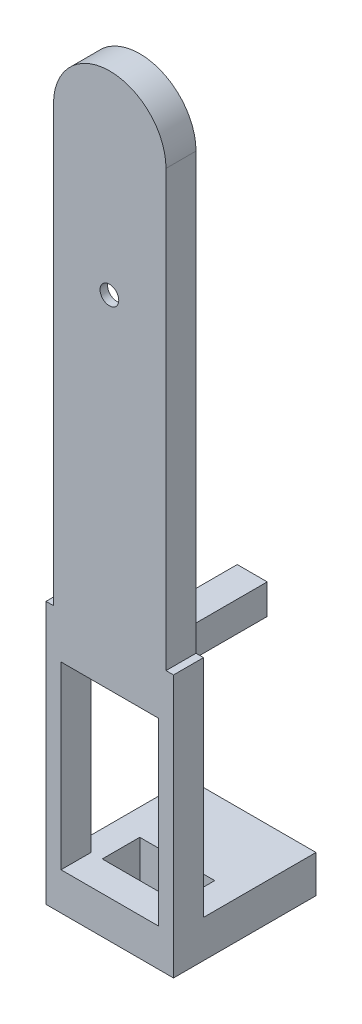
SolidWorks part; units mm, degrees
ref_plane "前基準面" through (0, 0, 0) normal (0, 0, 1) x (1, 0, 0)
ref_plane "上基準面" through (0, 0, 0) normal (0, 1, 0) x (1, 0, 0)
ref_plane "右基準面" through (0, 0, 0) normal (1, 0, 0) x (0, 0, -1)
sketch "草圖1" plane through (0, 0, 0) normal (0, 0, 1) x (1, 0, 0)
  line L0 (0, 0) -> (0, 4.6483) construction
  line L1 (7.5, 0) -> (7.5, 58)
  line L2 (7.5, 0) -> (-7.5, 0)
  line L3 (-7.5, 0) -> (-7.5, 58)
  arc A0 (7.5, 58) -> (-7.5, 58) centre (0, 58) ccw
  dimension "D1" = 7.5
  dimension "D2" = 58
extrude "填料-伸長1" add sketch "草圖1" along normal blind 4
sketch "草圖6" plane through (0, 0, 0) normal (0, 0, 1) x (1, 0, 0)
  line L0 (0, 62.3953) -> (0, -4.428) construction
  line L1 (0, -2.2) -> (0, 2.2) construction
  line L3 (8.5, 0) -> (-8.5, 0)
  line L4 (8.5, 0) -> (8.5, -35)
  line L5 (8.5, -35) -> (-8.5, -35)
  line L6 (-8.5, 0) -> (-8.5, -35)
  dimension "D1" = 17
  dimension "D2" = 8.5
  dimension "D3" = 35
extrude "填料-伸長2" add sketch "草圖6" along normal blind 4
sketch "草圖7" plane through (0, 0, 0) normal (0, 0, 1) x (1, 0, 0)
  line L0 (0, 64.1958) -> (0, -38.5274) construction
  line L1 (0, -10.45) -> (0, 10.45) construction
  line L3 (-6.5, -6) -> (6.5, -6)
  line L4 (-6.5, -6) -> (-6.5, -30)
  line L5 (-6.5, -30) -> (6.5, -30)
  line L6 (6.5, -6) -> (6.5, -30)
  line L7 (-8.5, -35) -> (8.5, -35) construction
  dimension "D1" = 6.5
  dimension "D2" = 13
  dimension "D3" = 24
  dimension "D4" = 5
extrude "除料-伸長3" cut sketch "草圖7" along normal blind 12.1
sketch "草圖8" plane through (0, 0, 0) normal (0, 0, 1) x (1, 0, 0)
  line L0 (0, 64.1958) -> (0, -34.8274) construction
  line L1 (0, -10.45) -> (0, 10.45) construction
  line L2 (0, 64.1958) -> (0, -39.0142) construction
  line L3 (6.5, -18) -> (-6.5, -18) construction
  line L4 (6.5, -30) -> (6.5, -6) construction
  line L5 (-6.5, -6) -> (-6.5, -30) construction
  line L6 (6.5, -6) -> (-6.5, -6) construction
  line L7 (2, -2) -> (-2, -2)
  line L8 (2, -2) -> (2, -6)
  line L9 (2, -6) -> (-2, -6)
  line L10 (-2, -2) -> (-2, -6)
  circle A0 centre (0, -4) radius 1.175
  dimension "D5" = 2.35
  dimension "D1" = 4
  dimension "D2" = 4
  dimension "D3" = 2
  dimension "D4" = 2
extrude "填料-伸長3" add sketch "草圖8" against normal blind 15
ref_plane "平面1" through (0, -35, 0) normal (0, 1, 0) x (1, 0, 0)
sketch "草圖9" plane through (0, -35, 0) normal (0, 1, 0) x (1, 0, 0)
  line L0 (0, 15.9246) -> (0, -4.8463) construction
  line L1 (0, -10.45) -> (0, 10.45) construction
  line L2 (-5, 0) -> (-5, 5)
  line L3 (7.5, 0) -> (-7.5, 0) construction
  line L4 (-5, 5) -> (5, 5)
  line L5 (-5, 0) -> (5, 0)
  line L6 (5, 0) -> (5, 5)
  line L12 (-8.5, 0) -> (8.5, 0)
  line L16 (8.5, 0) -> (8.5, 15)
  line L17 (8.5, 15) -> (-8.5, 15)
  line L19 (-8.5, 15) -> (-8.5, 0)
  point P12 (0, 0)
  point P13 (0, 5)
  point P20 (0, 0)
  point P21 (0, 15)
  point P25 (0, 0)
  point P26 (0, 15)
  dimension "D1" = 5
  dimension "D2" = 5
  dimension "D3" = 5
extrude "填料-伸長4" add sketch "草圖9" along normal blind 5
sketch "草圖10" plane through (0, 0, -15) normal (0, 0, -1) x (-1, 0, 0)
  line L0 (0, 0) -> (0, -35) construction
  line L1 (8.5, -35) -> (-8.5, -35) construction
  line L5 (8.538, -32.5) -> (-8.538, -32.5) construction
  circle A0 centre (0, -32.5) radius 1.175
  dimension "D2" = 2.35
  dimension "D1" = 2.5
extrude "除料-伸長4" cut sketch "草圖10" against normal blind 12.7 contours A0
sketch "草圖11" plane through (0, 0, 0) normal (0, 0, -1) x (-1, 0, 0)
  line L0 (5.0498, 39.6042) -> (2.4707, 21.7759)
  line L1 (5.0498, 39.6042) -> (2.4849, 57.1042)
  line L2 (-2.083, 57.1042) -> (-4.9502, 39.6042)
  line L3 (-4.9502, 39.6042) -> (-2.0924, 22.1042)
  arc A0 (-2.0924, 22.1042) -> (2.4707, 21.7759) centre (0.201, 22.1042) ccw
  arc A1 (-2.083, 57.1042) -> (2.4849, 57.1042) centre (0.201, 57.1042) cw
extrude "除料-伸長6" cut sketch "草圖11" against normal blind 3 contours L1 A1 L2 L3 A0 L0
sketch "草圖13" plane through (0, 0, 0) normal (0, 0, -1) x (-1, 0, 0)
  line L0 (-4.9502, 39.6042) -> (5.0498, 39.6042) construction
  line L1 (0.201, 59.3882) -> (0.0364, 19.8168) construction
  arc A0 (2.4849, 57.1042) -> (-2.083, 57.1042) centre (0.201, 57.1042) ccw construction
  arc A1 (-2.0924, 22.1042) -> (2.4707, 21.7759) centre (0.201, 22.1042) ccw construction
  circle A2 centre (0.0498, 39.6042) radius 1.25
  dimension "D1" = 2.5
extrude "除料-伸長7" cut sketch "草圖13" against normal blind 13 contours A2
